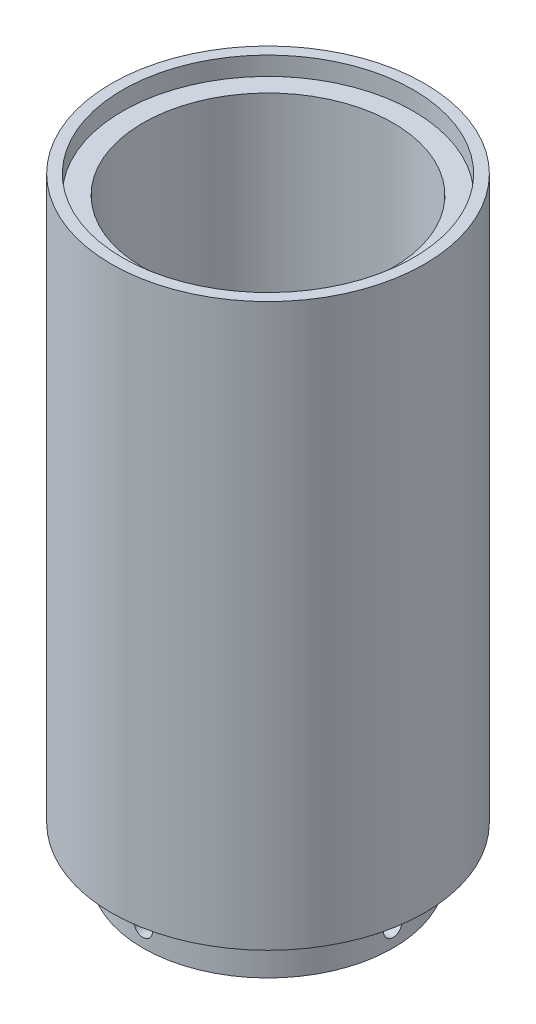
SolidWorks part; units mm, degrees
ref_plane "Front Plane" through (0, 0, 0) normal (0, 0, 1) x (1, 0, 0)
ref_plane "Top Plane" through (0, 0, 0) normal (0, 1, 0) x (1, 0, 0)
ref_plane "Right Plane" through (0, 0, 0) normal (1, 0, 0) x (0, 0, -1)
sketch "Sketch1" plane through (0, 0, 0) normal (0, 1, 0) x (1, 0, 0)
  circle A0 centre (0, 0) radius 33.85
  dimension "D1" = 67.7
extrude "Boss-Extrude1" add sketch "Sketch1" along normal blind 12.5
sketch "Sketch2" plane through (0, 0, 0) normal (1, 0, 0) x (0, 0, -1)
  line L0 (33.85, 12.5) -> (-33.85, 12.5) construction
  circle A0 centre (0, 5) radius 2.5
  dimension "D1" = 5
  dimension "D2" = 7.5
extrude "Cut-Extrude1" cut sketch "Sketch2" against normal through all both and the other way through all
sketch "Sketch3" plane through (0, 0, 0) normal (0, 0, 1) x (1, 0, 0)
  line L0 (33.85, 12.5) -> (-33.85, 12.5) construction
  circle A0 centre (0, 5) radius 2.5
  dimension "D1" = 5
  dimension "D2" = 7.5
extrude "Cut-Extrude2" cut sketch "Sketch3" against normal through all both and the other way through all
sketch "Sketch4" plane through (0, 12.5, 0) normal (0, 1, 0) x (1, 0, 0)
  circle A0 centre (0, 0) radius 42.35
  dimension "D1" = 84.7
extrude "Boss-Extrude2" add sketch "Sketch4" along normal blind 2
sketch "Sketch5" plane through (0, 14.5, 0) normal (0, 1, 0) x (1, 0, 0)
  circle A0 centre (0, 0) radius 33.85 construction
  circle A1 centre (0, 0) radius 42.35
  circle A2 centre (0, 0) radius 42.35
  circle A3 centre (0, 0) radius 33.85
  dimension "D1" = 0
extrude "Boss-Extrude3" add sketch "Sketch5" along normal blind 150
sketch "Sketch6" plane through (0, 164.5, 0) normal (0, 1, 0) x (1, 0, 0)
  line L0 (-39.35, 0) -> (-42.35, 0) construction
  circle A0 centre (0, 0) radius 39.35
  circle A1 centre (0, 0) radius 42.35 construction
  dimension "D1" = 78.7
extrude "Cut-Extrude3" cut sketch "Sketch6" against normal blind 5
ref_plane "Plane1" through (0, 12.5, 0) normal (0, 1, 0) x (1, 0, 0)
